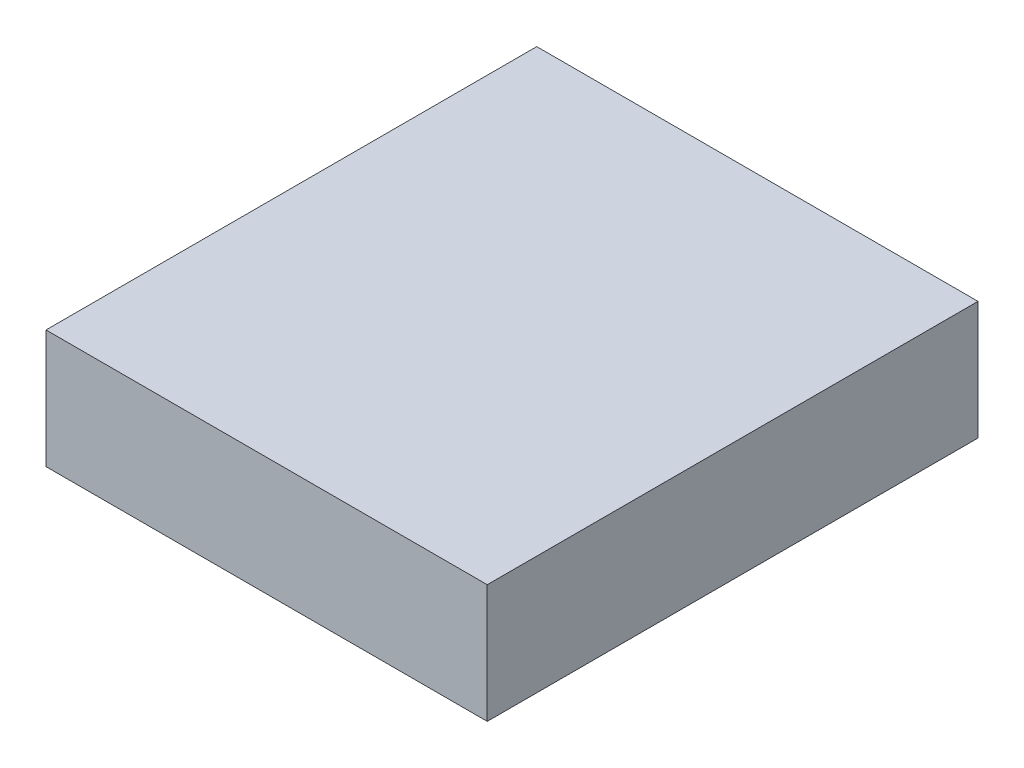
SolidWorks part; units mm, degrees
ref_plane "Alzado" through (0, 0, 0) normal (0, 0, 1) x (1, 0, 0)
ref_plane "Planta" through (0, 0, 0) normal (0, 1, 0) x (1, 0, 0)
ref_plane "Vista lateral" through (0, 0, 0) normal (1, 0, 0) x (0, 0, -1)
sketch "Croquis1" plane through (0, 0, 0) normal (0, 1, 0) x (1, 0, 0)
  line L1 (-26.035, -28.956) -> (26.035, -28.956)
  line L2 (-26.035, -28.956) -> (-26.035, 28.956)
  line L3 (-26.035, 28.956) -> (26.035, 28.956)
  line L4 (26.035, -28.956) -> (26.035, 28.956)
  line L5 (-26.035, -28.956) -> (26.035, 28.956) construction
  line L6 (-26.035, 28.956) -> (26.035, -28.956) construction
  point P0 (0, 0)
  dimension "D1" = 57.912
  dimension "D2" = 52.07
extrude "Saliente-Extruir1" add sketch "Croquis1" along normal mid plane 13.97
